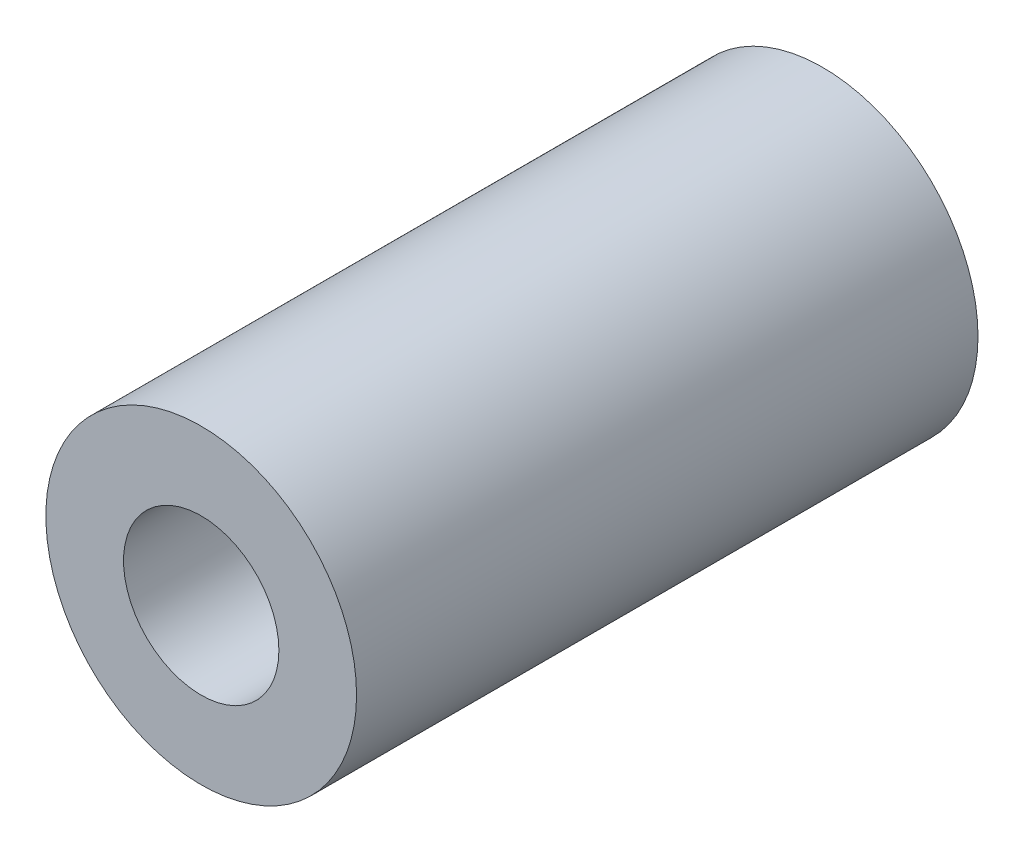
SolidWorks part; units mm, degrees
ref_plane "Front Plane" through (0, 0, 0) normal (0, 0, 1) x (1, 0, 0)
ref_plane "Top Plane" through (0, 0, 0) normal (0, 1, 0) x (1, 0, 0)
ref_plane "Right Plane" through (0, 0, 0) normal (1, 0, 0) x (0, 0, -1)
sketch "Sketch2" plane through (0, 0, 0) normal (0, 0, 1) x (1, 0, 0)
  circle A0 centre (0, 0) radius 10
  dimension "D1" = 20
extrude "Boss-Extrude1" add sketch "Sketch2" against normal blind 40
sketch "Sketch3" plane through (0, 0, 0) normal (0, 0, 1) x (1, 0, 0)
  circle A0 centre (0, 0) radius 5
  dimension "D1" = 10
extrude "Cut-Extrude1" cut sketch "Sketch3" against normal through all
